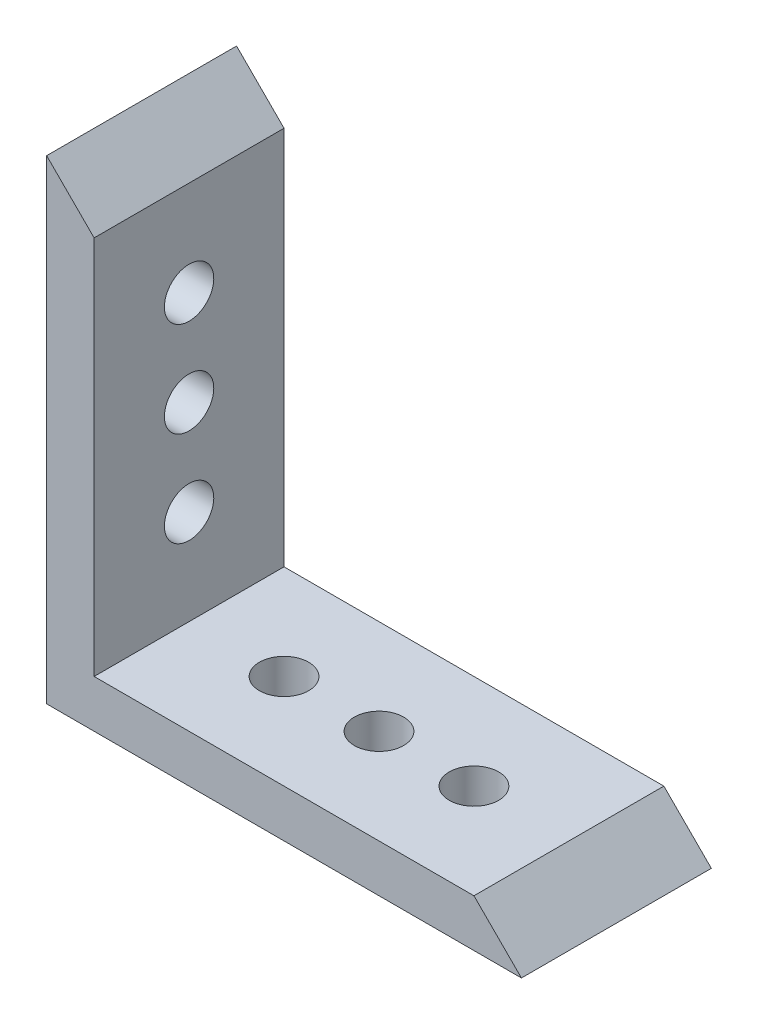
SolidWorks part; units mm, degrees
ref_plane "Front Plane" through (0, 0, 0) normal (0, 0, 1) x (1, 0, 0)
ref_plane "Top Plane" through (0, 0, 0) normal (0, 1, 0) x (1, 0, 0)
ref_plane "Right Plane" through (0, 0, 0) normal (1, 0, 0) x (0, 0, -1)
sketch "Sketch1" plane through (0, 0, 0) normal (0, 0, 1) x (1, 0, 0)
  line L0 (0, 0) -> (0, 50)
  line L1 (0, 50) -> (50, 0)
  line L2 (50, 0) -> (0, 0)
  dimension "D1" = 50
  dimension "D2" = 50
  dimension "D3" = 90
extrude "Boss-Extrude1" add sketch "Sketch1" along normal blind 20
sketch "Sketch2" plane through (0, 0, 20) normal (0, 0, 1) x (1, 0, 0)
  line L0 (5, 45) -> (5, 5)
  line L1 (50, 0) -> (0, 50) construction
  line L2 (5, 5) -> (45, 5)
  line L3 (0, 50) -> (0, 0) construction
  line L4 (0, 0) -> (50, 0) construction
  dimension "D1" = 5
  dimension "D2" = 5
extrude "Cut-Extrude1" cut sketch "Sketch2" against normal through all and the other way through all
sketch "Sketch4" plane through (5, 0, 0) normal (1, 0, 0) x (0, 0, -1)
  line L0 (-20, 45) -> (0, 45) construction
  circle A0 centre (-10, 35) radius 2.6
  circle A1 centre (-10, 25) radius 2.6
  circle A2 centre (-10, 15) radius 2.6
  dimension "D1" = 5.2
  dimension "D2" = 5.2
  dimension "D3" = 5.2
  dimension "D5" = 10
  dimension "D6" = 10
  dimension "D4" = 10
extrude "Cut-Extrude2" cut sketch "Sketch4" against normal through all contours A0 | A1 | A2
sketch "Sketch5" plane through (0, 5, 0) normal (0, 1, 0) x (1, 0, 0)
  line L0 (45, -20) -> (45, 0) construction
  circle A0 centre (35, -10) radius 2.6
  circle A1 centre (25, -10) radius 2.6
  circle A2 centre (15, -10) radius 2.6
  dimension "D1" = 5.2
  dimension "D2" = 5.2
  dimension "D3" = 5.2
  dimension "D5" = 10
  dimension "D6" = 10
  dimension "D4" = 10
extrude "Cut-Extrude3" cut sketch "Sketch5" against normal through all contours A2 | A1 | A0
